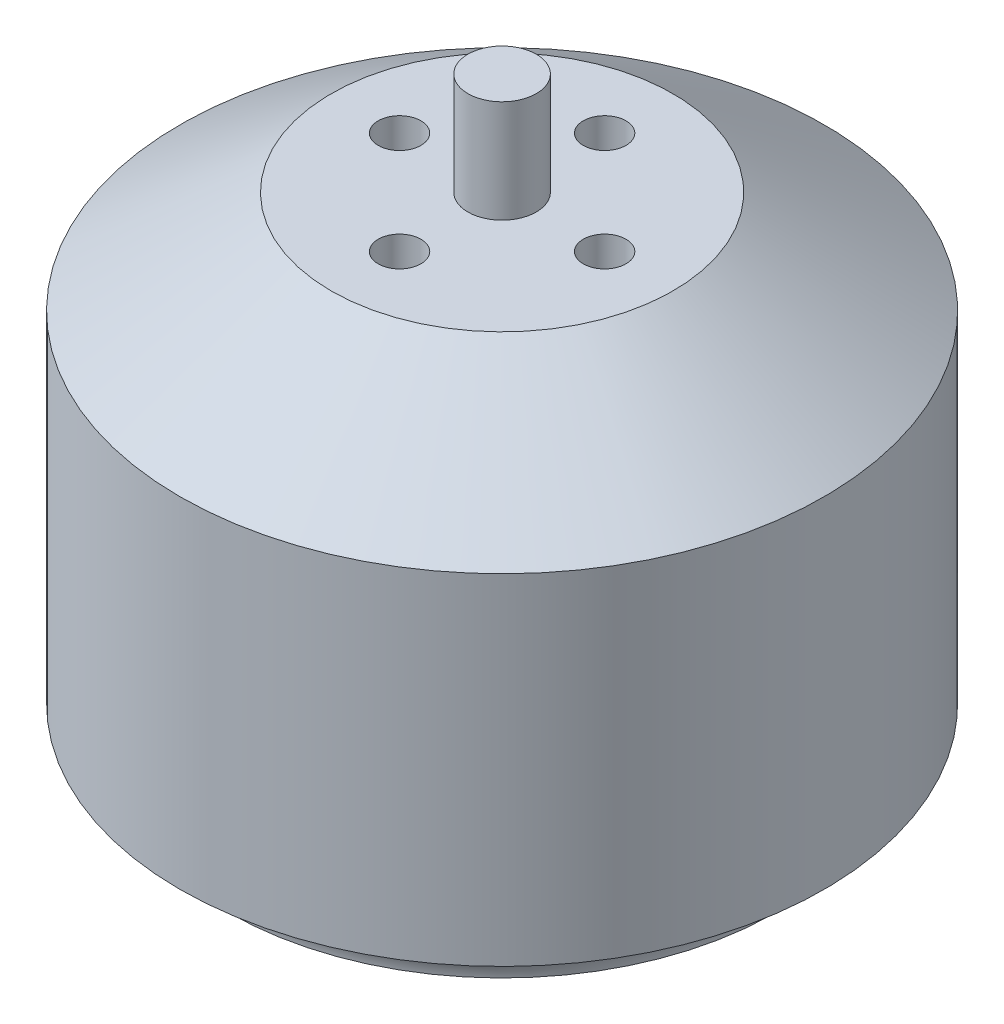
SolidWorks part; units mm, degrees
ref_plane "Front Plane" through (0, 0, 0) normal (0, 0, 1) x (1, 0, 0)
ref_plane "Top Plane" through (0, 0, 0) normal (0, 1, 0) x (1, 0, 0)
ref_plane "Right Plane" through (0, 0, 0) normal (1, 0, 0) x (0, 0, -1)
sketch "Sketch1" plane through (0, 0, 0) normal (0, 1, 0) x (1, 0, 0)
  circle A0 centre (0, 0) radius 18.85
  dimension "D1" = 37.7
extrude "Boss-Extrude1" add sketch "Sketch1" along normal blind 28.5
sketch "Sketch2" plane through (0, 28.5, 0) normal (0, 1, 0) x (1, 0, 0)
  circle A0 centre (0, 0) radius 2
  dimension "D1" = 4
extrude "Boss-Extrude2" add sketch "Sketch2" along normal blind 6
sketch "Sketch3" plane through (0, 0, 0) normal (0, -1, 0) x (1, 0, 0)
  circle A0 centre (0, 0) radius 2
  dimension "D1" = 4
extrude "Boss-Extrude3" add sketch "Sketch3" along normal blind 2.6
sketch "Sketch6" plane through (0, 0, 0) normal (0, -1, 0) x (1, 0, 0)
  line L0 (0, -2) -> (0, 2) construction
  line L1 (-8, 0) -> (0, 0) construction
  line L2 (0, 9.5) -> (0, 0) construction
  line L3 (-12.5, 0) -> (0, 0)
  circle A0 centre (8, 0) radius 1.75
  circle A1 centre (-8, 0) radius 1.75
  circle A2 centre (0, 9.5) radius 1.75
  circle A3 centre (0, -9.5) radius 1.75
  circle A4 centre (0, 0) radius 2 construction
  circle A5 centre (0, 0) radius 2 construction
  circle A6 centre (-12.5, 0) radius 1.75
  circle A7 centre (12.5, 0) radius 1.75
  dimension "D1" = 16
  dimension "D2" = 3.5
  dimension "D3" = 19
  dimension "D4" = 25
hole_wizard "M3x0.5 Tapped Hole1" positions "3DSketch2" profile "Sketch8" tap size "M3x0.5" standard "ANSI Metric"
sketch3d "3DSketch2"
  point P0 (0, 0, 9.5)
  point P3 (8, 0, 0)
  point P6 (12.5, 0, 0)
  point P9 (0, 0, -9.5)
  point P12 (-8, 0, 0)
  point P15 (-12.5, 0, 0)
sketch "Sketch8" plane through (0, 0, 9.5) normal (1, 0, 0) x (0, 0, -1)
  line L0 (0, 0) -> (0, 2.4)
  line L1 (0, 2.4) -> (1.25, 1.6489)
  line L2 (1.25, 1.6489) -> (1.25, 0)
  line L5 (1.25, 0) -> (0, 0)
  line L10 (0, 2.4) -> (-1.25, 1.6489) construction
  line L11 (0, -6.35) -> (0, 107.95) construction
  dimension "Tap Drill Dia." = 2.5
  dimension "Tap Drill Depth" = 2.4
  dimension "Drill Angle" = 118
cosmetic thread "Hole Thread1" parameters "D1"=1, "D2"=3
cosmetic thread "Hole Thread2" parameters "D1"=1, "D2"=3
cosmetic thread "Hole Thread3" parameters "D1"=1, "D2"=3
cosmetic thread "Hole Thread4" parameters "D1"=1, "D2"=3
cosmetic thread "Hole Thread5" parameters "D1"=1, "D2"=3
cosmetic thread "Hole Thread6" parameters "D1"=1, "D2"=3
sketch "Sketch10" plane through (0, 0, 0) normal (0, 0, 1) x (1, 0, 0)
  line L1 (18.85, 28.5) -> (-18.85, 28.5) construction
  line L3 (-18.85, 28.5) -> (-10, 28.5)
  line L4 (0, 28.5) -> (0, 0) construction
  line L6 (-10, 28.5) -> (-18.85, 22.5)
  line L7 (-18.85, 28.5) -> (-18.85, 0) construction
  line L8 (-18.85, 22.5) -> (-18.85, 28.5)
  line L9 (-18.85, 2.6) -> (-18.85, 0)
  line L10 (-18.85, 0) -> (-16, 0)
  line L11 (-18.85, 0) -> (18.85, 0) construction
  arc A1 (-18.85, 2.6) -> (-16, 0) centre (-18.85, -0.262) cw
  dimension "D1" = 10
  dimension "D2" = 6
  dimension "D3" = 16
  dimension "D4" = 2.6
revolve "Cut-Revolve1" cut sketch "Sketch10" angle 360 about L4
sketch "Sketch11" plane through (0, 28.5, 0) normal (0, 1, 0) x (1, 0, 0)
  line L0 (0, 6) -> (0, 0) construction
  circle A0 centre (0, 6) radius 2
  circle A1 centre (6, 0) radius 2
  circle A2 centre (0, -6) radius 2
  circle A3 centre (-6, 0) radius 2
  point P13 (0, 0)
  dimension "D1" = 4
  dimension "D2" = 6
  dimension "D3" = 4
  dimension "D4" = 6
  dimension "D5" = 6
hole_wizard "M3x0.5 Tapped Hole2" positions "3DSketch4" profile "Sketch13" tap size "M3x0.5" standard "ANSI Metric"
sketch3d "3DSketch4"
  line L0 (-12.5, 0, 0) -> (0, 0, 0) construction
  point P0 (0, 28.5, -6)
  point P3 (6, 28.5, 0)
  point P6 (0, 28.5, 6)
  point P9 (-6.25, 0, 0)
  point P13 (-6, 28.5, 0)
sketch "Sketch13" plane through (0, 28.5, -6) normal (1, 0, 0) x (0, 0, 1)
  line L0 (0, 0) -> (0, 6)
  line L1 (0, 6) -> (1.25, 5.2489)
  line L2 (1.25, 5.2489) -> (1.25, 0)
  line L5 (1.25, 0) -> (0, 0)
  line L10 (0, 6) -> (-1.25, 5.2489) construction
  line L11 (0, -6.35) -> (0, 107.95) construction
  dimension "Tap Drill Dia." = 2.5
  dimension "Tap Drill Depth" = 6
  dimension "Drill Angle" = 118
cosmetic thread "Hole Thread7" parameters "D1"=6, "D2"=3
cosmetic thread "Hole Thread8" parameters "D1"=6, "D2"=3
cosmetic thread "Hole Thread9" parameters "D1"=6, "D2"=3
cosmetic thread "Hole Thread10" parameters "D1"=6, "D2"=3
cosmetic thread "Hole Thread11" parameters "D1"=6, "D2"=3
